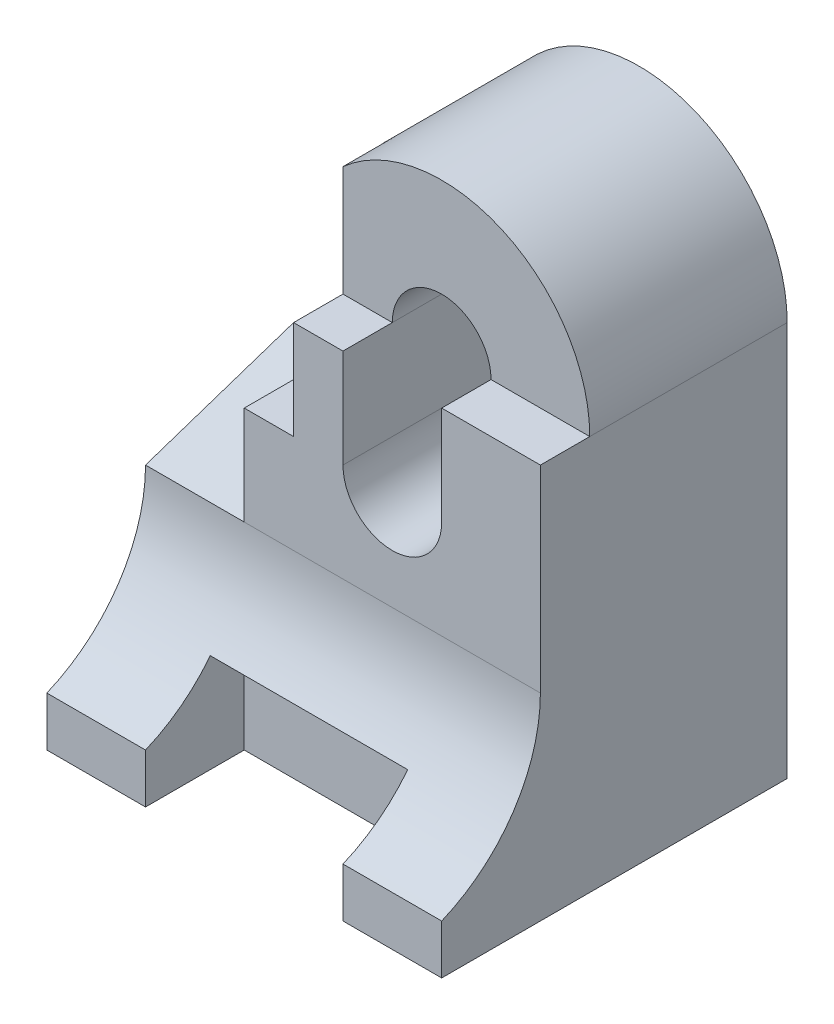
SolidWorks part; units mm, degrees
ref_plane "Front Plane" through (0, 0, 0) normal (0, 0, 1) x (1, 0, 0)
ref_plane "Top Plane" through (0, 0, 0) normal (0, 1, 0) x (1, 0, 0)
ref_plane "Right Plane" through (0, 0, 0) normal (1, 0, 0) x (0, 0, -1)
sketch "Sketch1" plane through (0, 0, 0) normal (0, 0, 1) x (1, 0, 0)
  line L0 (4, 2) -> (4, 6)
  line L1 (4, -2) -> (-4, -2)
  line L2 (4, -2) -> (4, 2)
  line L3 (-2, 2) -> (-4, 2)
  line L4 (-4, -2) -> (-4, 2)
  line L5 (4, -2) -> (-4, 2) construction
  line L6 (4, 2) -> (-4, -2) construction
  line L7 (-2, 2) -> (-2, 6)
  line L8 (1, 6) -> (1, 4) construction
  line L9 (2, 6) -> (2, 4)
  line L10 (0, 6) -> (0, 4)
  arc A0 (-2, 6) -> (4, 6) centre (1, 6) cw
  arc A1 (2, 6) -> (0, 6) centre (1, 6) ccw
  arc A2 (0, 4) -> (2, 4) centre (1, 4) ccw
  point P0 (0, 0)
  point P10 (1, 5)
  dimension "D7" = 2
  dimension "D1" = 4
  dimension "D2" = 8
  dimension "D3" = 4
  dimension "D4" = 4
  dimension "D5" = 2
  dimension "D6" = 1
  dimension "D8" = 6
extrude "Boss-Extrude2" add sketch "Sketch1" along normal blind 5
sketch "Sketch2" plane through (4, 0, 0) normal (1, 0, 0) x (0, 0, -1)
  line L0 (-5, -2) -> (-7, -2)
  line L1 (-7, -2) -> (-7, -1)
  line L2 (-5, -2) -> (-5, 6) construction
  line L3 (-5, 2) -> (-5, -2)
  arc A0 (-7, -1) -> (-5, 2) centre (-8.25, 2) ccw
  dimension "D1" = 1
  dimension "D2" = 2
extrude "Boss-Extrude3" add sketch "Sketch2" against normal blind 8
sketch "Sketch4" plane through (0, -2, 0) normal (0, -1, 0) x (1, 0, 0)
  line L0 (2, 7) -> (2, 5)
  line L1 (-4, 7) -> (4, 7) construction
  line L2 (2, 5) -> (-2, 5)
  line L3 (-2, 5) -> (-2, 7)
  line L4 (-2, 7) -> (2, 7)
  dimension "D1" = 2
  dimension "D2" = 2
  dimension "D3" = 2
extrude "Cut-Extrude2" cut sketch "Sketch4" against normal blind 2
sketch "Sketch5" plane through (0, 0, 5) normal (0, 0, 1) x (1, 0, 0)
  line L0 (4, 6) -> (2, 6)
  line L1 (0, 6) -> (-2, 6)
  arc A0 (4, 6) -> (-2, 6) centre (1, 6) ccw construction
  arc A1 (0, 6) -> (2, 6) centre (1, 6) cw
  arc A2 (4, 6) -> (-2, 6) centre (1, 6) ccw
  arc A3 (2, 6) -> (0, 6) centre (1, 6) ccw construction
extrude "Cut-Extrude3" cut sketch "Sketch5" against normal blind 1
sketch "Sketch6" plane through (0, 0, 5) normal (0, 0, 1) x (1, 0, 0)
  line L0 (-2, 4) -> (-1, 4)
  line L1 (-2, 6) -> (-2, 2) construction
  line L2 (-1, 4) -> (-1, 8.2361)
  line L3 (-2, 4) -> (-2, 6)
  arc A0 (4, 6) -> (-2, 6) centre (1, 6) ccw construction
  arc A1 (-1, 8.2361) -> (-2, 6) centre (1, 6) ccw
  dimension "D1" = 2
  dimension "D2" = 1
extrude "Cut-Extrude4" cut sketch "Sketch6" against normal blind 2
sketch "Sketch7" plane through (0, 0, 0) normal (0, 0, -1) x (-1, 0, 0)
  line L0 (4, 2) -> (4, 3)
  line L1 (4, 3) -> (2, 6)
  line L2 (2, 6) -> (2, 2)
  line L3 (2, 2) -> (4, 2)
  dimension "D1" = 1
extrude "Boss-Extrude4" add sketch "Sketch7" against normal blind 1
sketch "Sketch8" plane through (-2, 0, 0) normal (-1, 0, 0) x (0, 0, 1)
  line L0 (1, 2) -> (1, 3)
  line L1 (1, 6) -> (1, 2) construction
  line L2 (1, 3) -> (2, 3)
  line L3 (2, 3) -> (5, 2)
  line L4 (5, 2) -> (1, 2)
  dimension "D1" = 1
  dimension "D2" = 1
extrude "Boss-Extrude5" add sketch "Sketch8" along normal blind 2
